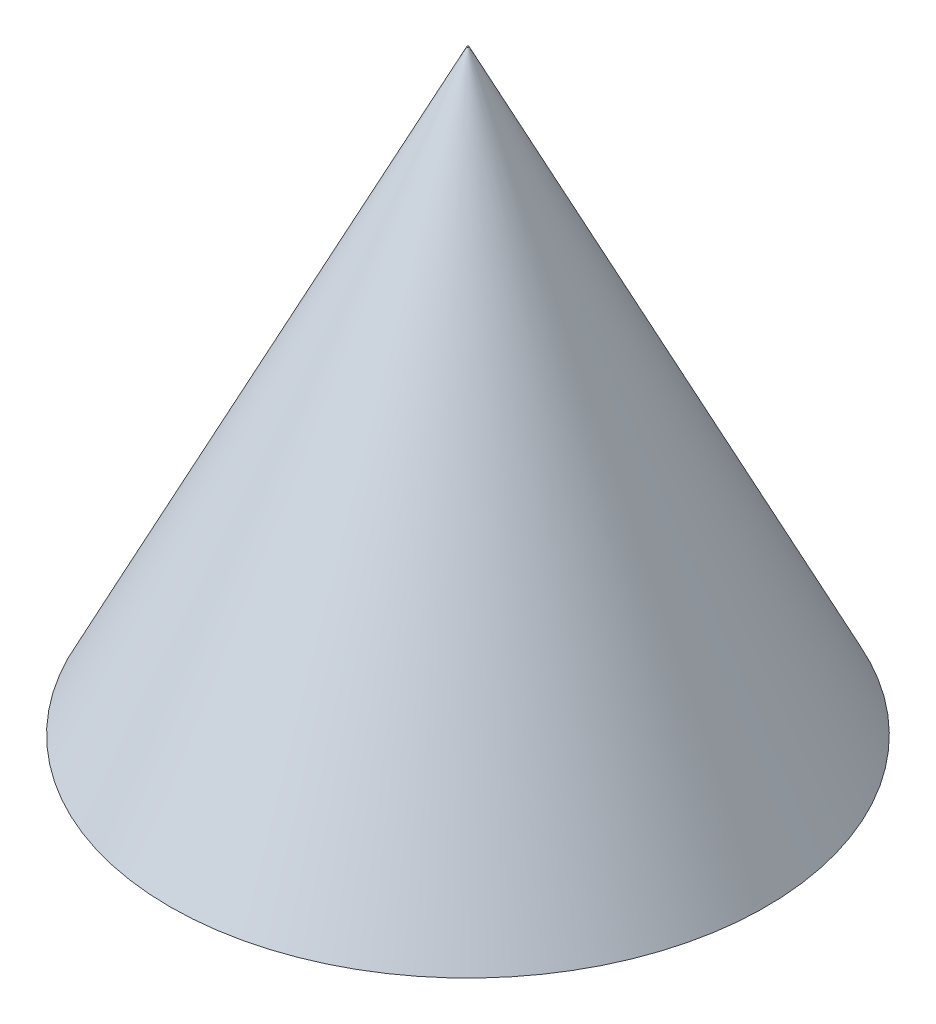
SolidWorks part; units mm, degrees
ref_plane "Plan de face" through (0, 0, 0) normal (0, 0, 1) x (1, 0, 0)
ref_plane "Plan de dessus" through (0, 0, 0) normal (0, 1, 0) x (1, 0, 0)
ref_plane "Plan de droite" through (0, 0, 0) normal (1, 0, 0) x (0, 0, -1)
sketch "Esquisse1" plane through (0, 0, 0) normal (0, 1, 0) x (1, 0, 0)
  circle A0 centre (0, 0) radius 29
extrude "Boss.-Extru.1" add sketch "Esquisse1" along normal blind 58 draft 26.5
